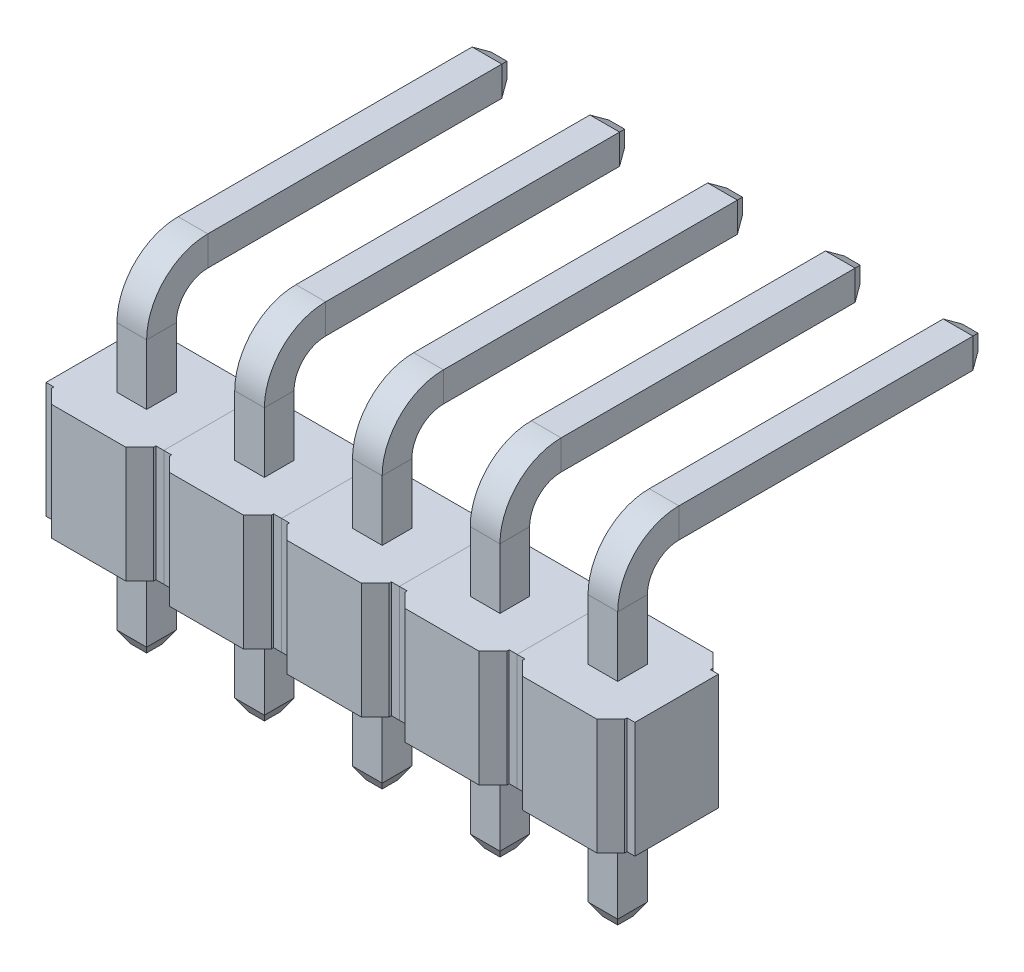
SolidWorks part; units mm, degrees
ref_plane "Front" through (0, 0, 0) normal (0, 0, 1) x (1, 0, 0)
ref_plane "Top" through (0, 0, 0) normal (0, 1, 0) x (1, 0, 0)
ref_plane "Right" through (0, 0, 0) normal (1, 0, 0) x (0, 0, -1)
sketch "Эскиз2" plane through (0, 0, 0) normal (1, 0, 0) x (0, 0, -1)
  line L0 (0, 0) -> (0, -2.2)
  line L1 (0, 0) -> (0, 3.8)
  line L2 (1, 4.8) -> (7.6, 4.8)
  arc A0 (1, 4.8) -> (0, 3.8) centre (1, 3.8) ccw
  point P7 (0, 4.8)
  dimension "D4" = 1
  dimension "D1" = 2.2
  dimension "D2" = 4.8
  dimension "D3" = 7.6
sketch "Эскиз3" plane through (0, 0, 0) normal (0, 1, 0) x (1, 0, 0)
  line L1 (-0.32, -0.32) -> (0.32, -0.32)
  line L2 (-0.32, -0.32) -> (-0.32, 0.32)
  line L3 (-0.32, 0.32) -> (0.32, 0.32)
  line L4 (0.32, -0.32) -> (0.32, 0.32)
  line L5 (-0.32, -0.32) -> (0.32, 0.32) construction
  line L6 (-0.32, 0.32) -> (0.32, -0.32) construction
  point P0 (0, 0)
sweep "По траектории1" add profiles "Эскиз3" path "Эскиз2"
chamfer "Фаска1" distance 0.15 angle 60 8 edges at (0, -2.2, -0.32) (-0.32, -2.2, 0) (0, -2.2, 0.32) (0.32, -2.2, 0) (0, 5.12, -7.6) (-0.32, 4.8, -7.6) (0, 4.48, -7.6) (0.32, 4.8, -7.6)
sketch "Эскиз4" plane through (0, 0, 0) normal (0, 1, 0) x (1, 0, 0)
  line L0 (-1.1, 0.9) -> (-1.1, 1.25)
  line L1 (-1.1, -1.25) -> (1.1, -1.25)
  line L2 (-1.1, -1.25) -> (-1.1, -0.9)
  line L3 (-1.1, 1.25) -> (1.1, 1.25)
  line L4 (1.1, -1.25) -> (1.1, -0.9)
  line L5 (-1.1, -1.25) -> (1.1, 1.25) construction
  line L6 (-1.1, 1.25) -> (1.1, -1.25) construction
  line L7 (-1.27, -0.9) -> (-1.1, -0.9)
  line L8 (-1.27, -0.9) -> (-1.27, 0.9)
  line L9 (-1.27, 0.9) -> (-1.1, 0.9)
  line L10 (1.27, -0.9) -> (1.27, 0.9)
  line L11 (-1.27, -0.9) -> (1.27, 0.9) construction
  line L12 (-1.27, 0.9) -> (1.27, -0.9) construction
  line L13 (1.1, 0.9) -> (1.1, 1.25)
  line L14 (1.1, -0.9) -> (1.27, -0.9)
  line L15 (1.1, 0.9) -> (1.27, 0.9)
  point P0 (0, 0)
  point P5 (0, 0)
  dimension "D1" = 2.2
  dimension "D2" = 2.5
  dimension "D3" = 1.8
  dimension "D4" = 2.54
extrude "Бобышка-Вытянуть1" add sketch "Эскиз4" along normal blind 2.5 separate body
chamfer "Фаска2" distance 0.3 angle 45 4 edges at (-1.1, 1.25, -1.25) (1.1, 1.25, -1.25) (-1.1, 1.25, 1.25) (1.1, 1.25, 1.25)
pattern_linear "Линейный массив1" count 5 spacing 2.54 along (-1, 0, 0) of bodies 102 101
ref_plane "Pin Midplane" through (0, 4.8, 0) normal (0, 1, 0) x (1, 0, 0)
